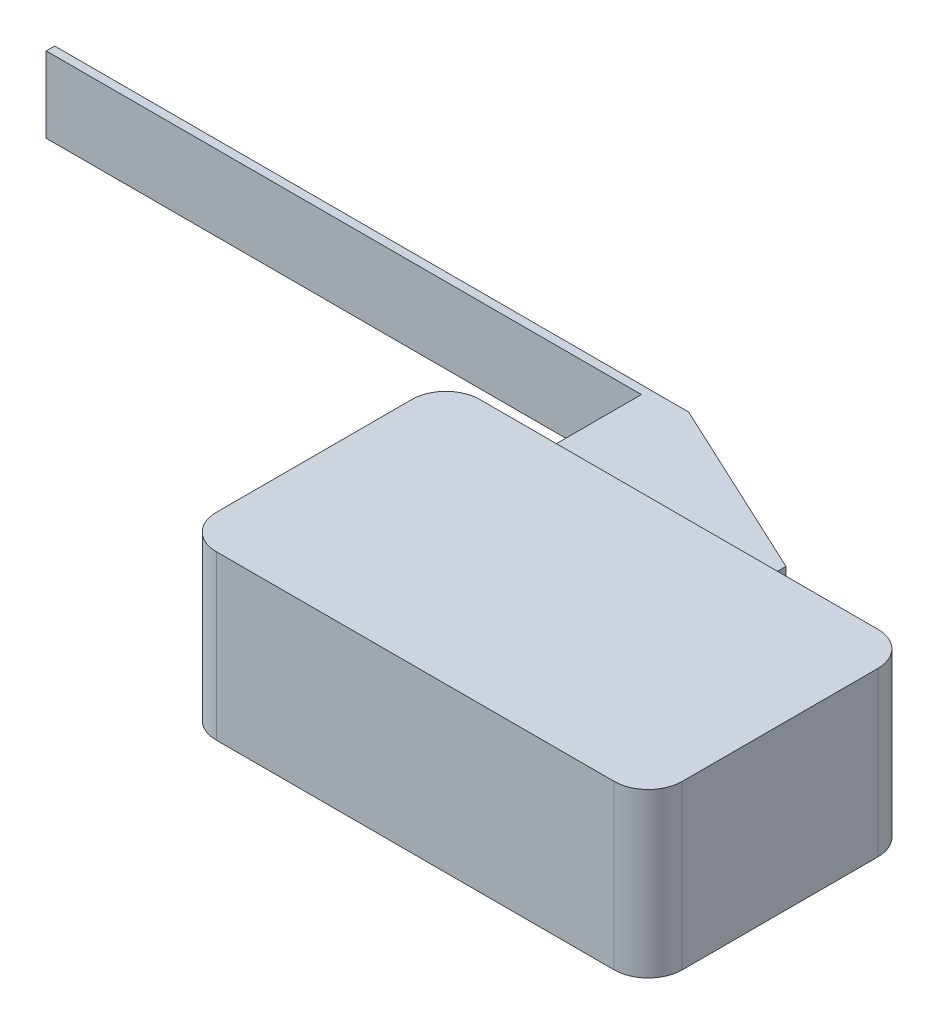
SolidWorks part; units mm, degrees
ref_plane "Front Plane" through (0, 0, 0) normal (0, 0, 1) x (1, 0, 0)
ref_plane "Top Plane" through (0, 0, 0) normal (0, 1, 0) x (1, 0, 0)
ref_plane "Right Plane" through (0, 0, 0) normal (1, 0, 0) x (0, 0, -1)
sketch "Sketch1" plane through (0, 0, 0) normal (0, 1, 0) x (1, 0, 0)
  line L1 (0, 0) -> (27.4, 0)
  line L2 (0, 0) -> (0, 15.5)
  line L3 (0, 15.5) -> (27.4, 15.5)
  line L4 (27.4, 0) -> (27.4, 15.5)
  dimension "D1" = 15.5
  dimension "D2" = 27.4
extrude "Boss-Extrude1" add sketch "Sketch1" along normal blind 9.6
fillet "Fillet1" radius 2 4 edges at (0, 4.8, -15.5) (27.4, 4.8, -15.5) (0, 4.8, 0) (27.4, 4.8, 0)
sketch "Sketch2" plane through (0, 0, -15.5) normal (0, 0, -1) x (-1, 0, 0)
  line L0 (-25.4, 9.6) -> (-2, 9.6) construction
  line L1 (-4, 2.65) -> (-17, 2.65)
  line L2 (-4, 2.65) -> (-4, 7.1)
  line L3 (-4, 7.1) -> (-17, 7.1)
  line L4 (-17, 2.65) -> (-17, 7.1)
  line L6 (0, 9.6) -> (0, 0) construction
  dimension "D1" = 4.45
  dimension "D2" = 2.5
  dimension "D3" = 13
  dimension "D4" = 4
extrude "Boss-Extrude2" add sketch "Sketch2" along normal blind 8
sketch "Sketch3" plane through (4, 0, 0) normal (-1, 0, 0) x (0, 0, 1)
  line L0 (-23.5, 7.1) -> (-15.5, 7.1) construction
  line L1 (-23.5, 2.65) -> (-23, 2.65)
  line L2 (-23.5, 2.65) -> (-23.5, 7.1)
  line L3 (-23.5, 7.1) -> (-23, 7.1)
  line L4 (-23, 2.65) -> (-23, 7.1)
  dimension "D1" = 0.5
extrude "Boss-Extrude3" add sketch "Sketch3" along normal blind 35
chamfer "Chamfer1" distance 5 angle 65 1 edges at (17, 4.875, -23.5)
